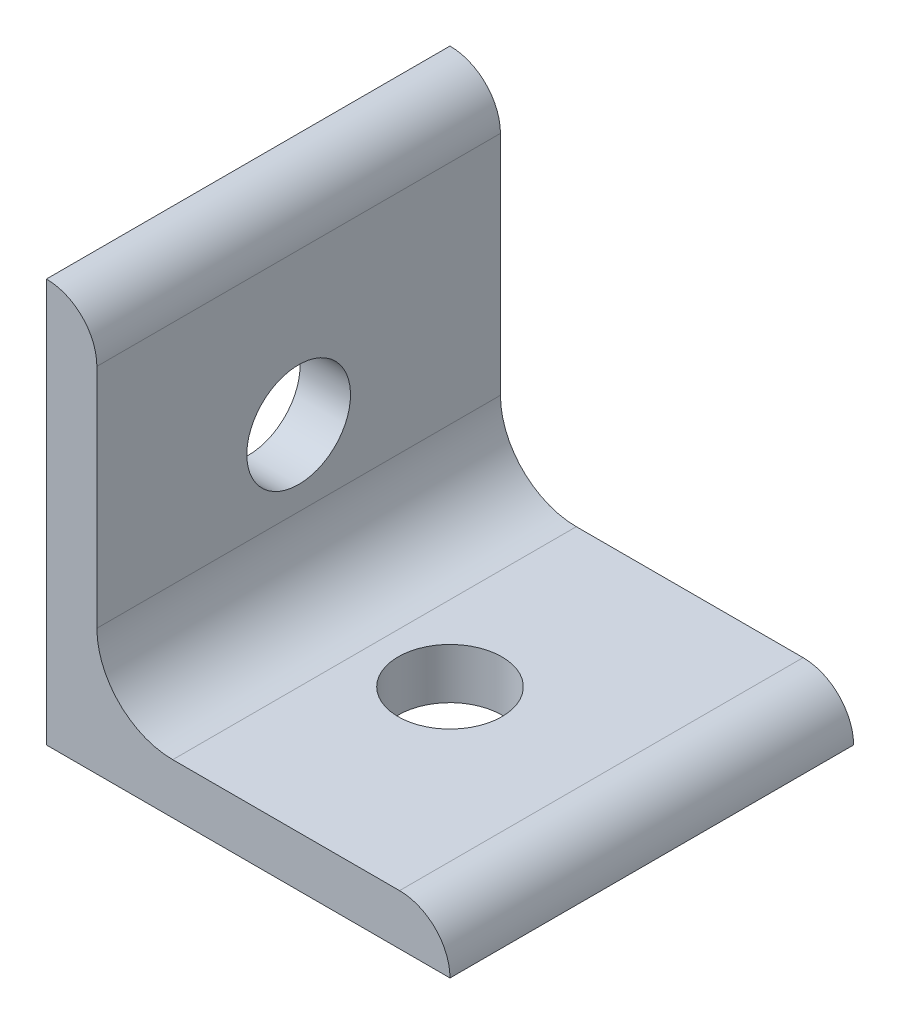
SolidWorks part; units mm, degrees
material "6105-T5 Aluminum"
ref_plane "Front Plane" through (0, 0, 0) normal (0, 0, 1) x (1, 0, 0)
ref_plane "Top Plane" through (0, 0, 0) normal (0, 1, 0) x (1, 0, 0)
ref_plane "Right Plane" through (0, 0, 0) normal (1, 0, 0) x (0, 0, -1)
sketch "Sketch1" plane through (0, 0, 0) normal (0, 0, 1) x (1, 0, 0)
  line L0 (23.473, -1.6964) -> (23.473, -27.0964)
  line L3 (26.648, -19.1462) -> (26.648, -4.8714)
  line L5 (45.698, -23.9214) -> (31.4232, -23.9214)
  line L7 (23.473, -27.0964) -> (48.873, -27.0964)
  arc A3 (23.473, -1.6964) -> (26.648, -4.8714) centre (23.473, -4.8714) cw
  arc A4 (31.4232, -23.9214) -> (26.648, -19.1462) centre (31.4232, -19.1462) cw
  arc A5 (45.698, -23.9214) -> (48.873, -27.0964) centre (45.698, -27.0964) cw
extrude "Extrude1" add sketch "Sketch1" along normal blind 25.4
sketch "Sketch2" plane through (23.473, 0, 0) normal (-1, 0, 0) x (0, 0, 1)
  circle A0 centre (12.7, -14.3964) radius 3.2639
extrude "Cut-Extrude1" cut sketch "Sketch2" against normal through all
sketch "Sketch3" plane through (0, -27.0964, 0) normal (0, -1, 0) x (1, 0, 0)
  circle A0 centre (36.173, 12.7) radius 3.2639
extrude "Cut-Extrude2" cut sketch "Sketch3" against normal through all
